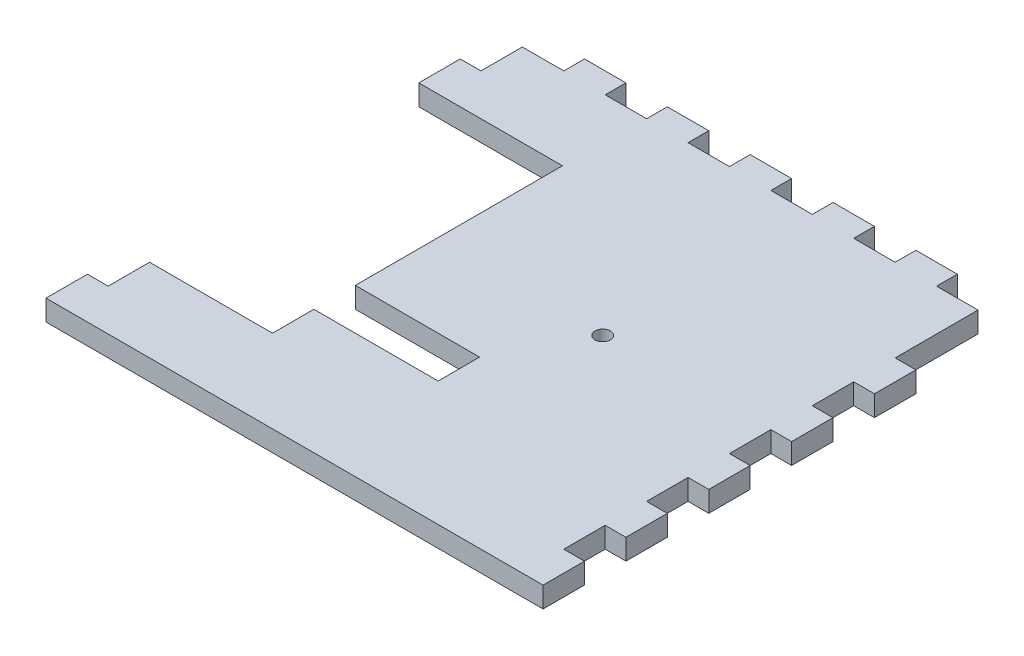
SolidWorks part; units mm, degrees
ref_plane "Front Plane" through (0, 0, 0) normal (0, 0, 1) x (1, 0, 0)
ref_plane "Top Plane" through (0, 0, 0) normal (0, 1, 0) x (1, 0, 0)
ref_plane "Right Plane" through (0, 0, 0) normal (1, 0, 0) x (0, 0, -1)
sketch "Sketch1" plane through (0, 0, 0) normal (0, 1, 0) x (1, 0, 0)
  line L1 (-139.7, -139.7) -> (139.7, -139.7)
  line L2 (-139.7, -139.7) -> (-139.7, 139.7)
  line L3 (-139.7, 139.7) -> (139.7, 139.7)
  line L4 (139.7, -139.7) -> (139.7, 139.7)
  line L5 (-139.7, -139.7) -> (139.7, 139.7) construction
  line L6 (-139.7, 139.7) -> (139.7, -139.7) construction
  point P0 (0, 0)
  dimension "D1" = 279.4
  dimension "D2" = 279.4
extrude "Boss-Extrude1" add sketch "Sketch1" along normal blind 12.7
sketch "Sketch2" plane through (139.7, 0, 0) normal (1, 0, 0) x (0, 0, -1)
  line L5 (153.67, 0) -> (-153.67, 0) construction
  line L6 (-139.7, 0) -> (-114.3, 0)
  line L7 (-139.7, 0) -> (-139.7, 12.7)
  line L8 (-139.7, 12.7) -> (-114.3, 12.7)
  line L9 (-114.3, 0) -> (-114.3, 12.7)
  line L10 (-139.7, 12.7) -> (139.7, 12.7) construction
  line L12 (-139.7, 12.7) -> (-139.7, 0) construction
  dimension "D1" = 25.4
extrude "Boss-Extrude2" add sketch "Sketch2" along normal blind 12.7
pattern_linear "LPattern1" count 5 spacing 50.8 along (0, 0, -1) of "Boss-Extrude2"
mirror "Mirror1" about plane through (0, 0, 0) normal (1, 0, 0) of "LPattern1", "Boss-Extrude2"
sketch "Sketch3" plane through (0, 0, -139.7) normal (0, 0, -1) x (-1, 0, 0)
  line L0 (-139.7, 12.7) -> (139.7, 12.7) construction
  line L1 (-114.3, 12.7) -> (-88.9, 12.7)
  line L2 (-114.3, 12.7) -> (-114.3, 0)
  line L3 (-114.3, 0) -> (-88.9, 0)
  line L4 (-88.9, 12.7) -> (-88.9, 0)
  line L5 (-139.7, 0) -> (139.7, 0) construction
  line L6 (-152.4, 0) -> (-152.4, 12.7) construction
  dimension "D1" = 38.1
  dimension "D2" = 25.4
extrude "Boss-Extrude3" add sketch "Sketch3" along normal blind 12.7
pattern_linear "LPattern2" count 5 spacing 50.8 along (-1, 0, 0) of "Boss-Extrude3"
sketch "Sketch6" plane through (0, 12.7, 0) normal (0, 1, 0) x (1, 0, 0)
  line L0 (38.1, 139.7) -> (12.7, 139.7) construction
  line L1 (139.7, -12.7) -> (139.7, 12.7) construction
  circle A0 centre (38.1, 11.176) radius 4.7625
  dimension "D1" = 128.524
  dimension "D3" = 9.525
  dimension "D2" = 101.6
extrude "Cut-Extrude1" cut sketch "Sketch6" against normal through all
sketch "Sketch8" plane through (0, 12.7, 0) normal (0, 1, 0) x (1, 0, 0)
  line L1 (-152.4, 88.9) -> (-64.3339, 88.9)
  line L2 (-152.4, 88.9) -> (-152.4, -88.9)
  line L3 (-152.4, -88.9) -> (-64.3339, -88.9)
  line L4 (-64.3339, 88.9) -> (-64.3339, -88.9)
  line L6 (-152.4, 88.9) -> (-139.7, 88.9) construction
  dimension "D1" = 177.8
extrude "Cut-Extrude3" cut sketch "Sketch8" against normal through all
sketch "Sketch7" plane through (0, 12.7, 0) normal (0, 1, 0) x (1, 0, 0)
  line L2 (-114.3, 139.7) -> (-139.7, 139.7) construction
  line L3 (-139.7, 139.7) -> (-139.7, 88.9) construction
  circle A0 centre (-101.6, 65.278) radius 5.08
  circle A1 centre (-101.6, 27.686) radius 5.08
  dimension "D1" = 10.16
  dimension "D2" = 10.16
  dimension "D3" = 38.1
  dimension "D5" = 37.592
  dimension "D6" = 74.422
sketch "Sketch9" plane through (-139.7, 0, 0) normal (-1, 0, 0) x (0, 0, 1)
  line L0 (160.655, 0) -> (-160.655, 0) construction
  line L1 (-88.9, 12.7) -> (-114.3, 12.7)
  line L2 (-88.9, 12.7) -> (-88.9, 0)
  line L3 (-88.9, 0) -> (-114.3, 0)
  line L4 (-114.3, 12.7) -> (-114.3, 0)
  dimension "D1" = 25.4
extrude "Boss-Extrude4" add sketch "Sketch9" along normal blind 12.7
sketch "Sketch11" plane through (-64.3339, 0, 0) normal (-1, 0, 0) x (0, 0, 1)
  line L6 (88.9, 0) -> (-88.9, 0) construction
  line L7 (63.5, 0) -> (38.1, 0)
  line L8 (63.5, 0) -> (63.5, 12.7)
  line L9 (63.5, 12.7) -> (38.1, 12.7)
  line L10 (38.1, 0) -> (38.1, 12.7)
  line L11 (88.9, 12.7) -> (-88.9, 12.7) construction
  line L12 (88.9, 0) -> (88.9, 12.7) construction
  dimension "D1" = 25.4
  dimension "D2" = 25.4
extrude "Cut-Extrude4" cut sketch "Sketch11" against normal blind 76.2
